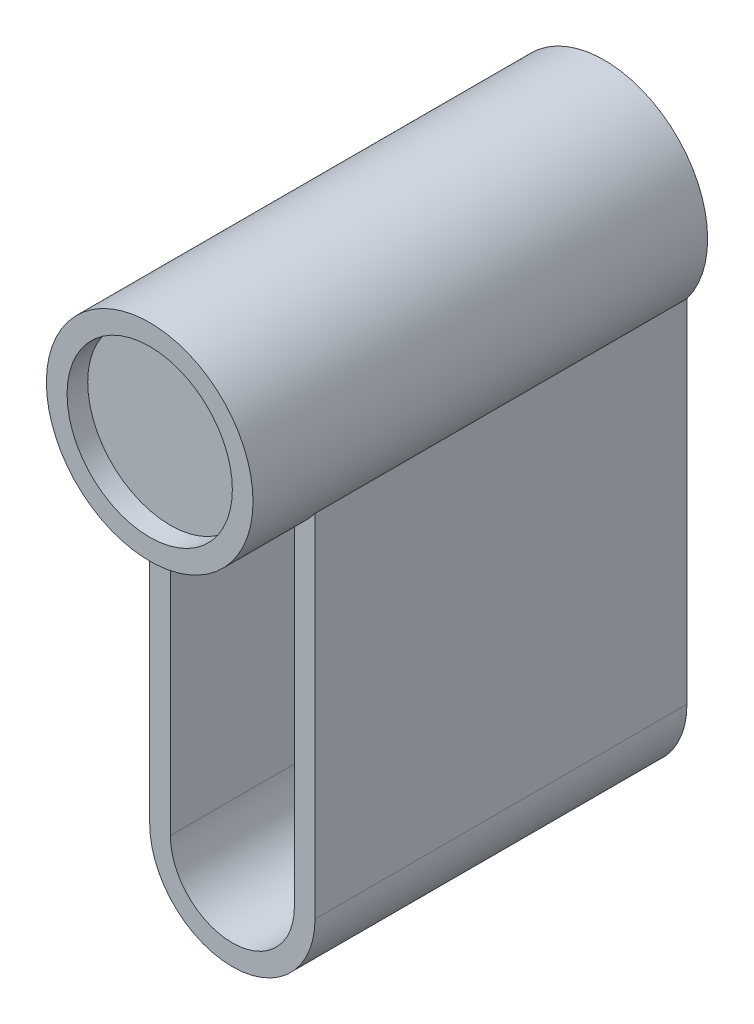
SolidWorks part; units mm, degrees
ref_plane "Front Plane" through (0, 0, 0) normal (0, 0, 1) x (1, 0, 0)
ref_plane "Top Plane" through (0, 0, 0) normal (0, 1, 0) x (1, 0, 0)
ref_plane "Right Plane" through (0, 0, 0) normal (1, 0, 0) x (0, 0, -1)
sketch "Sketch1" plane through (0, 0, 0) normal (0, 0, 1) x (1, 0, 0)
  circle A0 centre (0, 0) radius 25
  dimension "D1" = 50
extrude "Extrude1" add sketch "Sketch1" along normal blind 110
sketch "Sketch2" plane through (0, 0, 110) normal (0, 0, 1) x (1, 0, 0)
  circle A0 centre (0, 0) radius 20
  dimension "D1" = 40
extrude "Extrude2" cut sketch "Sketch2" against normal blind 5
sketch "Sketch3" plane through (0, 0, 0) normal (0, 0, 1) x (1, 0, 0)
  line L0 (0, 0) -> (0, -100) construction
  line L1 (-20, -100) -> (20, -100) construction
  line L2 (-20, -100) -> (-20, 0)
  line L3 (-20, 0) -> (20, 0)
  line L4 (20, 0) -> (20, -100)
  arc A0 (-20, -100) -> (20, -100) centre (0, -100) ccw
  dimension "D1" = 20
  dimension "D2" = 100
extrude "Extrude3" add sketch "Sketch3" along normal blind 90
sketch "Sketch4" plane through (0, 0, 90) normal (0, 0, 1) x (1, 0, 0)
  line L4 (-15, -20) -> (-15, -100)
  line L5 (15, -100) -> (15, -20)
  circle A0 centre (0, 0) radius 25 construction
  arc A2 (-15, -20) -> (15, -20) centre (0, 0) ccw
  arc A4 (-15, -100) -> (15, -100) centre (0, -100) ccw
extrude "Extrude4" cut sketch "Sketch4" against normal through all
